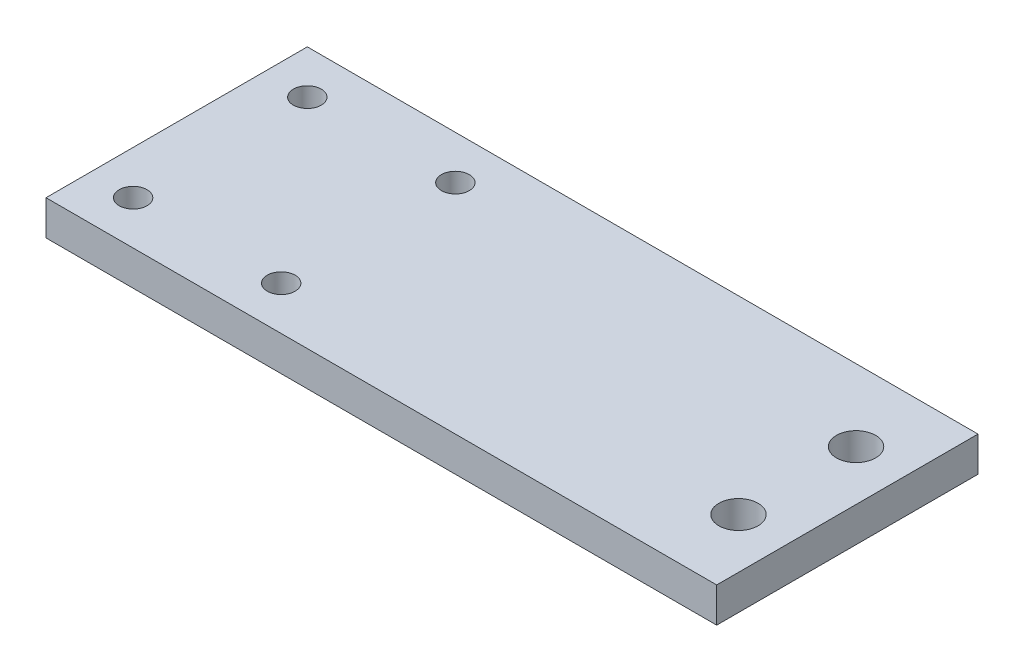
SolidWorks part; units mm, degrees
ref_plane "前视基准面" through (0, 0, 0) normal (0, 0, 1) x (1, 0, 0)
ref_plane "上视基准面" through (0, 0, 0) normal (0, 1, 0) x (1, 0, 0)
ref_plane "右视基准面" through (0, 0, 0) normal (1, 0, 0) x (0, 0, -1)
sketch "草图1" plane through (0, 0, 0) normal (0, 1, 0) x (1, 0, 0)
  line L0 (-42, 10) -> (35, 10) construction
  line L2 (35, -5) -> (35, 25)
  line L4 (-42, -5) -> (-42, 25)
  line L5 (-3.5, 30) -> (-3.5, -10) construction
  line L6 (-42, 25) -> (35, 25)
  line L7 (-42, -5) -> (35, -5)
  circle A0 centre (-20, 20) radius 1.6
  circle A1 centre (-37, 20) radius 1.6
  circle A2 centre (-20, 0) radius 1.6
  circle A3 centre (-37, 0) radius 1.6
  circle A8 centre (29.25, 16.75) radius 2.25
  circle A9 centre (29.25, 3.25) radius 2.25
  point P0 (0, 0)
  dimension "D3" = 5
  dimension "D4" = 22
  dimension "D7" = 4.5
  dimension "D5" = 10
  dimension "D6" = 10
  dimension "D8" = 5.75
  dimension "D9" = 6.75
  dimension "D10" = 15
extrude "凸台-拉伸1" add sketch "草图1" along normal blind 4
